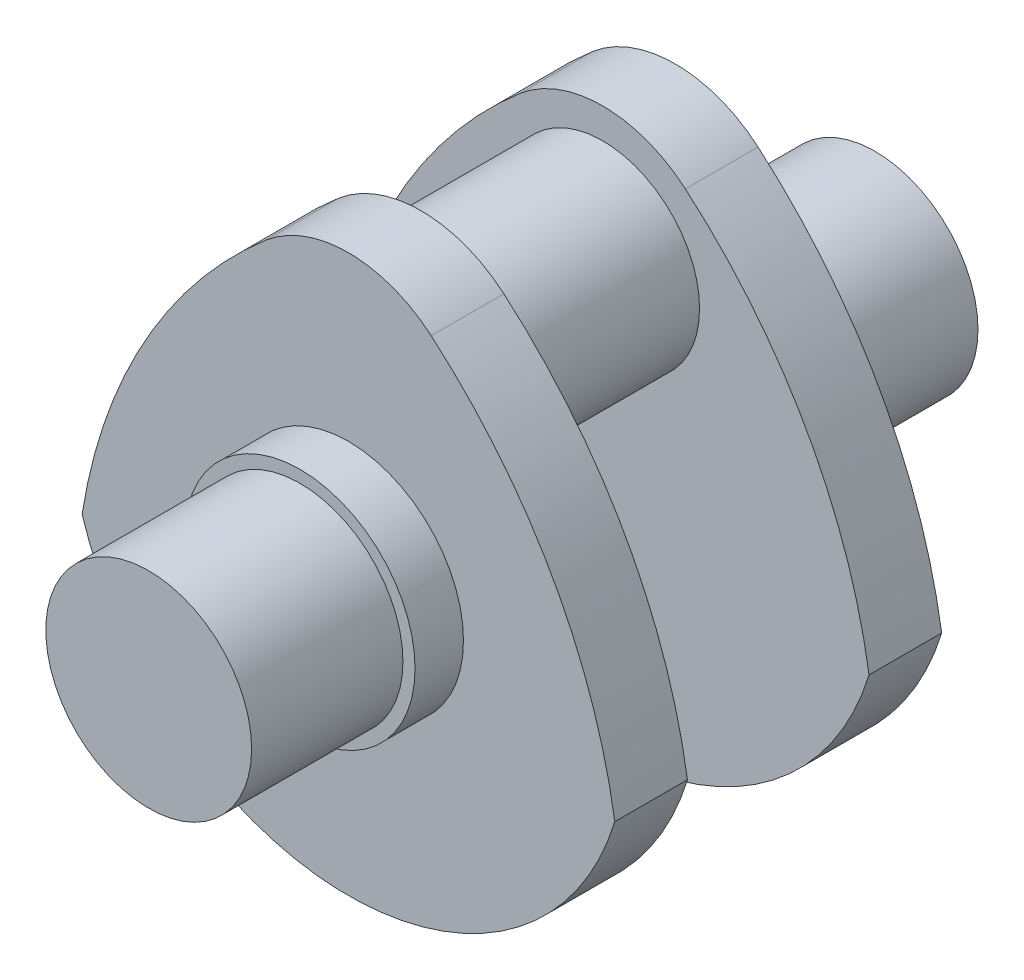
SolidWorks part; units mm, degrees
ref_plane "Front Plane" through (0, 0, 0) normal (0, 0, 1) x (1, 0, 0)
ref_plane "Top Plane" through (0, 0, 0) normal (0, 1, 0) x (1, 0, 0)
ref_plane "Right Plane" through (0, 0, 0) normal (1, 0, 0) x (0, 0, -1)
sketch "Sketch1" plane through (0, 0, 0) normal (0, 0, 1) x (1, 0, 0)
  circle A0 centre (0, 0) radius 17
  dimension "D1" = 34
extrude "Boss-Extrude1" add sketch "Sketch1" along normal blind 25
sketch "Sketch2" plane through (0, 0, 0) normal (0, 0, 1) x (1, 0, 0)
  circle A0 centre (0, 0) radius 19
  dimension "D1" = 38
extrude "Boss-Extrude2" add sketch "Sketch2" against normal blind 8
sketch "Sketch5" plane through (0, 0, -8) normal (0, 0, -1) x (-1, 0, 0)
  arc A0 (44, -13.4164) -> (-44, -13.4164) centre (0, 0) cw
  arc A1 (13.6681, 40.9431) -> (-13.6681, 40.9431) centre (0, 25) ccw
  arc A2 (-44, -13.4164) -> (-13.6681, 40.9431) centre (44.9095, -27.3845) cw
  arc A3 (13.6681, 40.9431) -> (44, -13.4164) centre (-44.9095, -27.3845) cw
  dimension "D2" = 46
  dimension "D3" = 42
  dimension "D5" = 90
  dimension "D6" = 90
  dimension "D1" = 88
  dimension "D4" = 25
extrude "Boss-Extrude3" add sketch "Sketch5" along normal blind 12
sketch "Sketch6" plane through (0, 0, -20) normal (0, 0, -1) x (-1, 0, 0)
  circle A0 centre (0, 25) radius 16
  point P2 (0, 0)
  dimension "D1" = 32
  dimension "D2" = 25
extrude "Boss-Extrude4" add sketch "Sketch6" along normal blind 15
mirror "Mirror2" about plane through (0, 25, -35) normal (0, 0, -1) of bodies 104
